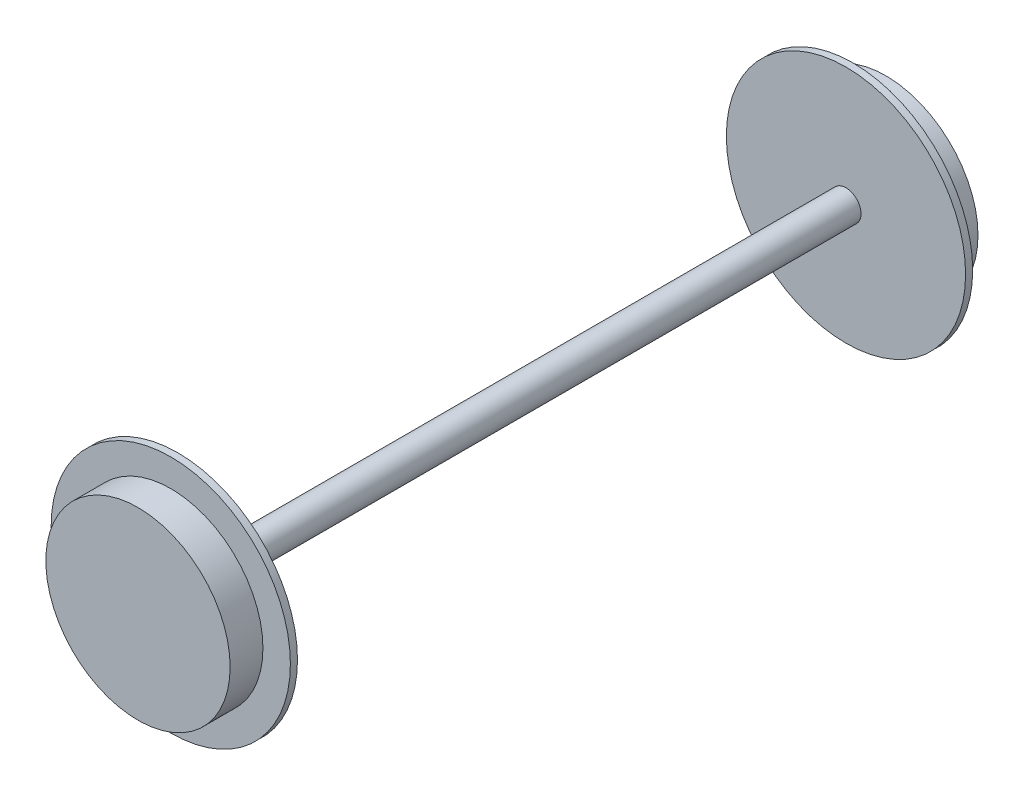
SolidWorks part; units mm, degrees
ref_plane "Спереди" through (0, 0, 0) normal (0, 0, 1) x (1, 0, 0)
ref_plane "Сверху" through (0, 0, 0) normal (0, 1, 0) x (1, 0, 0)
ref_plane "Справа" through (0, 0, 0) normal (1, 0, 0) x (0, 0, -1)
other "Configuration Table"
sketch "Эскиз1" plane through (0, 0, 0) normal (1, 0, 0) x (0, 0, -1)
  line L0 (214.1624, 0) -> (-183.9442, 0) construction
  line L1 (0, 134.9276) -> (0, -130.3597) construction
  line L2 (0, 8.5) -> (188.5, 8.5)
  line L3 (188.5, 8.5) -> (188.5, 67.5)
  line L4 (188.5, 67.5) -> (192.5, 67.5)
  line L5 (192.5, 67.5) -> (192.5, 52)
  line L6 (192.5, 52) -> (211, 52)
  line L7 (211, 52) -> (211, 0)
  line L8 (0, 8.5) -> (0, 0)
  line L9 (0, 0) -> (211, 0)
  dimension "D1" = 211
  dimension "D2" = 8.5
  dimension "D3" = 67.5
  dimension "D4" = 52
  dimension "D5" = 22.5
  dimension "D6" = 4
revolve "Повернуть2" add sketch "Эскиз1" angle 360 about L9
mirror "Зеркальное отражение1" about plane through (0, 8.5, 0) normal (0, 0, -1) of "Повернуть2"
